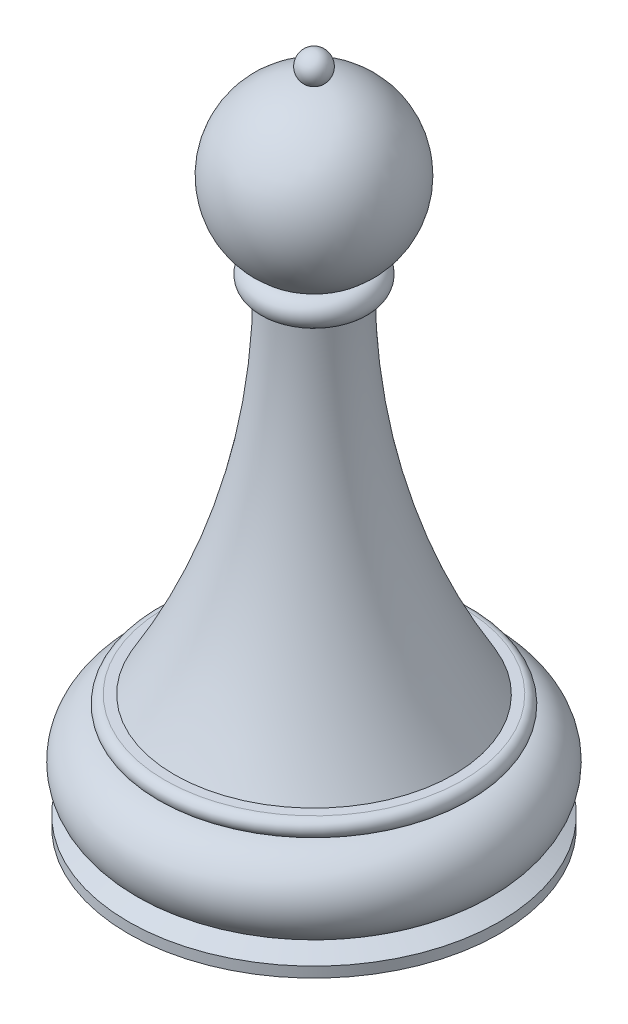
SolidWorks part; units mm, degrees
ref_plane "Front Plane" through (0, 0, 0) normal (0, 0, 1) x (1, 0, 0)
ref_plane "Top Plane" through (0, 0, 0) normal (0, 1, 0) x (1, 0, 0)
ref_plane "Right Plane" through (0, 0, 0) normal (1, 0, 0) x (0, 0, -1)
sketch "Sketch1" plane through (0, 0, 0) normal (0, 0, 1) x (1, 0, 0)
  line L0 (0, 0) -> (0, -19.2438) construction
  line L1 (0, 0) -> (12.5016, 0)
  line L2 (12.4781, -1.4284) -> (12.4781, -1.4347)
  line L3 (0, -9.6219) -> (15.5627, -9.6219)
  line L4 (15.5627, -9.6219) -> (15.5627, -8.7515)
  line L5 (15.5627, -8.7515) -> (13.8939, -7.9606)
  line L6 (0, 0) -> (0, -9.6219)
  line L7 (0, -9.6219) -> (0, 44.7444) construction
  line L8 (0, 47.2289) -> (0, 44.7444) construction
  line L9 (0, 44.7444) -> (0, 0)
  line L10 (3.1361, 29.503) -> (3.1361, 29.3567)
  line L11 (3.1361, 29.3567) -> (3.635, 29.3567)
  line L12 (0, 57.2082) -> (0, 47.2289) construction
  line L14 (0, 44.3858) -> (0, 46.811)
  arc A0 (12.5016, 0) -> (12.4781, -1.4284) centre (12.5016, -0.7144) cw
  arc A1 (13.8939, -7.9606) -> (12.4781, -1.4347) centre (12.4226, -4.8633) ccw
  arc A2 (3.6296, 31.6354) -> (0, 44.7444) centre (0, 37.6874) ccw
  arc A3 (3.6296, 31.6354) -> (3.1361, 29.503) centre (3.6296, 30.512) cw
  arc A4 (3.635, 29.3567) -> (11.7053, 0) centre (61.0646, 29.3567) ccw
  arc A5 (0, 44.3858) -> (0, 46.811) centre (0, 45.5984) ccw
  point P14 (0, 45.5984)
  dimension "D1" = 0.0064
  dimension "D4" = 0.7144
  dimension "D3" = 3.429
  dimension "D7" = 7.057
  dimension "D6" = 2.4252
  dimension "D2" = 12.5016
  dimension "D5" = 9.6219
revolve "Revolve1" add sketch "Sketch1" angle 360 about L0
